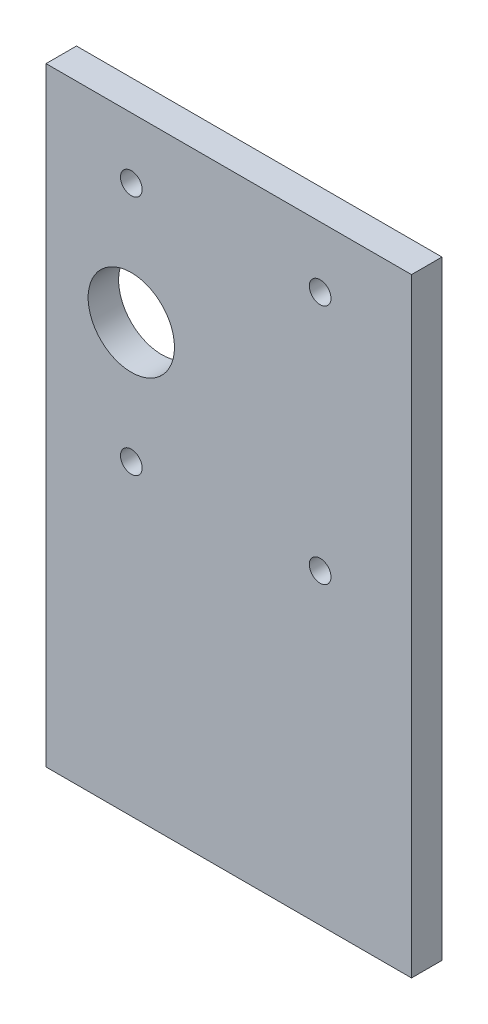
SolidWorks part; units mm, degrees
ref_plane "Front Plane" through (0, 0, 0) normal (0, 0, 1) x (1, 0, 0)
ref_plane "Top Plane" through (0, 0, 0) normal (0, 1, 0) x (1, 0, 0)
ref_plane "Right Plane" through (0, 0, 0) normal (1, 0, 0) x (0, 0, -1)
sketch "Sketch1" plane through (0, 0, 0) normal (0, 0, 1) x (1, 0, 0)
  line L1 (-17.8109, 11.7463) -> (20.2891, 11.7463)
  line L2 (-17.8109, 11.7463) -> (-17.8109, -51.7537)
  line L3 (-17.8109, -51.7537) -> (20.2891, -51.7537)
  line L4 (20.2891, 11.7463) -> (20.2891, -51.7537)
  dimension "D1" = 38.1
  dimension "D2" = 63.5
extrude "Boss-Extrude1" add sketch "Sketch1" along normal blind 3.175
sketch "Sketch2" plane through (0, 0, 3.175) normal (0, 0, 1) x (1, 0, 0)
  line L0 (20.2891, 11.7463) -> (-17.8109, 11.7463) construction
  line L1 (10.7641, 5.3963) -> (-8.9209, 5.3963)
  line L2 (10.7641, 5.3963) -> (10.7641, -19.7497)
  line L3 (10.7641, -19.7497) -> (-8.9209, -19.7497)
  line L4 (-8.9209, 5.3963) -> (-8.9209, -19.7497)
  line L5 (20.2891, -51.7537) -> (20.2891, 11.7463) construction
  dimension "D1" = 25.146
  dimension "D2" = 19.685
  dimension "D3" = 6.35
  dimension "D4" = 9.525
hole_wizard "#4-40 Tapped Holes" positions "Sketch3" profile "Sketch4" tap size "#4-40" standard "ANSI Inch" end condition through all
sketch "Sketch3" plane through (0, 0, 3.175) normal (0, 0, 1) x (1, 0, 0)
  point P0 (-8.9209, -19.7497)
  point P3 (10.7641, -19.7497)
  point P6 (10.7641, 5.3963)
  point P9 (-8.9209, 5.3963)
sketch "Sketch4" plane through (-8.9209, -19.7497, 3.175) normal (1, 0, 0) x (0, -1, 0)
  line L0 (0, 0) -> (0, 3.175)
  line L1 (0, 3.175) -> (1.1303, 3.175)
  line L2 (1.1303, 3.175) -> (1.1303, 0)
  line L5 (1.1303, 0) -> (0, 0)
  line L11 (0, -6.35) -> (0, 107.95) construction
  dimension "Thru Tap Drill Dia." = 2.2606
  dimension "Thru Tap Drill Depth" = 3.175
cosmetic thread "Hole Thread1" parameters "D2"=2.8448
cosmetic thread "Hole Thread2" parameters "D2"=2.8448
cosmetic thread "Hole Thread3" parameters "D2"=2.8448
cosmetic thread "Hole Thread4" parameters "D2"=2.8448
sketch "Sketch5" plane through (0, 0, 3.175) normal (0, 0, 1) x (1, 0, 0)
  line L0 (-8.9209, 5.3963) -> (-8.9209, -19.7497) construction
  circle A0 centre (-8.9209, -7.1767) radius 4.5
  point P0 (-8.9209, -7.1767)
  dimension "D1" = 9
extrude "Cut-Extrude1" cut sketch "Sketch5" against normal blind 3.175 contours A0
